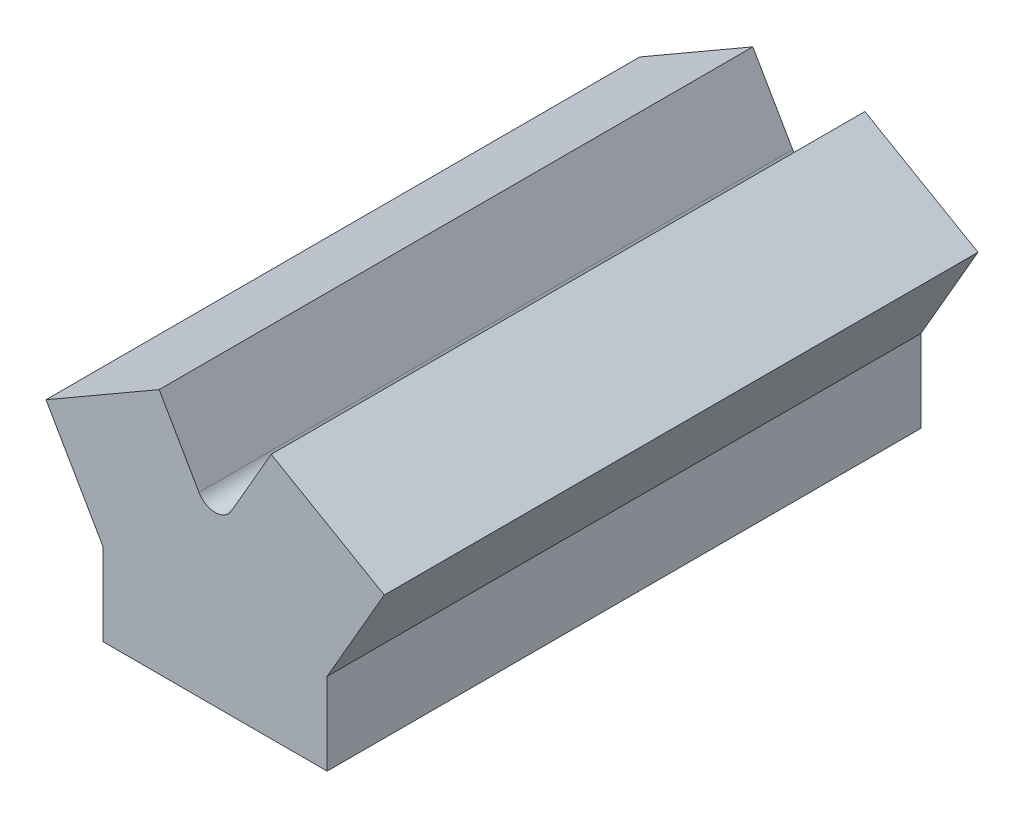
SolidWorks part; units mm, degrees
ref_plane "Front Plane" through (0, 0, 0) normal (0, 0, 1) x (1, 0, 0)
ref_plane "Top Plane" through (0, 0, 0) normal (0, 1, 0) x (1, 0, 0)
ref_plane "Right Plane" through (0, 0, 0) normal (1, 0, 0) x (0, 0, -1)
sketch "Sketch1" plane through (0, 0, 0) normal (0, 0, 1) x (1, 0, 0)
  line L0 (-10.9985, 120.65) -> (-38.1141, 167.6156)
  line L1 (-38.1141, 167.6156) -> (-115.0614, 123.19)
  line L2 (-115.0614, 123.19) -> (-76.2, 55.88)
  line L3 (-76.2, 55.88) -> (-76.2, 0)
  line L4 (-76.2, 0) -> (76.2, 0)
  line L5 (76.2, 0) -> (76.2, 55.88)
  line L6 (76.2, 55.88) -> (115.0614, 123.19)
  line L7 (115.0614, 123.19) -> (38.1141, 167.6156)
  line L8 (38.1141, 167.6156) -> (10.9985, 120.65)
  line L9 (0, 0) -> (0, 203.2754) construction
  arc A0 (-10.9985, 120.65) -> (10.9985, 120.65) centre (0, 127) ccw
  dimension "D2" = 25.4
  dimension "D1" = 127
  dimension "D3" = 30
  dimension "D4" = 123.19
  dimension "D5" = 55.88
  dimension "D6" = 152.4
extrude "Boss-Extrude1" add sketch "Sketch1" against normal blind 403.86
sketch "Sketch3" plane through (82.1082, 142.2156, 0) normal (0.5, 0.866, 0) x (0.866, -0.5, 0)
  line L1 (38.0511, 0) -> (-50.8, 0) construction
  circle A0 centre (-6.3744, 119.38) radius 22.86
  circle A1 centre (-6.3744, 231.14) radius 22.86
  circle A2 centre (-6.3744, 342.9) radius 22.86
  point P6 (-6.3744, 0)
  dimension "D1" = 119.38
  dimension "D2" = 45.72
  dimension "D3" = 45.72
  dimension "D5" = 45.72
  dimension "D4" = 111.76
  dimension "D6" = 111.76
extrude "Cut-Extrude1" cut sketch "Sketch3" against normal through all from offset 19.05 offset against normal yes
sketch "Sketch4" plane through (-82.1082, 142.2156, 0) normal (-0.5, 0.866, 0) x (0.866, 0.5, 0)
  line L2 (50.8, 0) -> (-38.0511, 0) construction
  circle A0 centre (6.3744, 63.5) radius 22.86
  circle A1 centre (6.3744, 175.26) radius 22.86
  circle A2 centre (6.3744, 287.02) radius 22.86
  point P2 (0, 0)
  point P6 (6.3744, 0)
  dimension "D1" = 45.72
  dimension "D2" = 63.5
  dimension "D3" = 45.72
  dimension "D5" = 45.72
  dimension "D4" = 111.76
  dimension "D6" = 111.76
extrude "Cut-Extrude2" cut sketch "Sketch4" against normal through all from offset 19.05 offset against normal yes
sketch "Sketch5" plane through (0, 0, 0) normal (0, 0, 1) x (1, 0, 0)
  line L0 (-50.8, 0) -> (-50.8, 31.75)
  line L1 (-76.2, 0) -> (76.2, 0) construction
  line L2 (-50.8, 31.75) -> (-26.3115, 45.814)
  line L3 (50.8, 0) -> (50.8, 31.75)
  line L4 (50.8, 31.75) -> (26.3115, 45.814)
  line L5 (-76.2, 55.88) -> (-76.2, 0) construction
  line L6 (76.2, 0) -> (76.2, 55.88) construction
  line L7 (50.8, 0) -> (-50.8, 0)
  arc A0 (26.3115, 45.814) -> (-26.3115, 45.814) centre (0, 0) ccw
  point P1 (-86.5725, 43.3508)
  dimension "D1" = 105.664
  dimension "D2" = 25.4
  dimension "D3" = 25.4
  dimension "D4" = 31.75
  dimension "D5" = 31.75
extrude "Cut-Extrude4" cut sketch "Sketch5" against normal blind 353.06 from offset 25.4 offset against normal yes
sketch "Sketch7" plane through (0, 0, 0) normal (0, -1, 0) x (1, 0, 0)
  line L0 (-76.2, -403.86) -> (76.2, -403.86) construction
  line L1 (-76.2, -403.86) -> (-76.2, 0) construction
  line L2 (-76.2, 0) -> (76.2, 0) construction
  line L3 (76.2, -403.86) -> (76.2, 0) construction
  circle A0 centre (-63.5, -391.16) radius 6.35
  circle A1 centre (63.5, -12.7) radius 6.35
  dimension "D1" = 12.7
  dimension "D4" = 12.7
  dimension "D2" = 12.7
  dimension "D3" = 12.7
  dimension "D5" = 12.7
  dimension "D6" = 12.7
extrude "Cut-Extrude5" cut sketch "Sketch7" against normal blind 76.2
